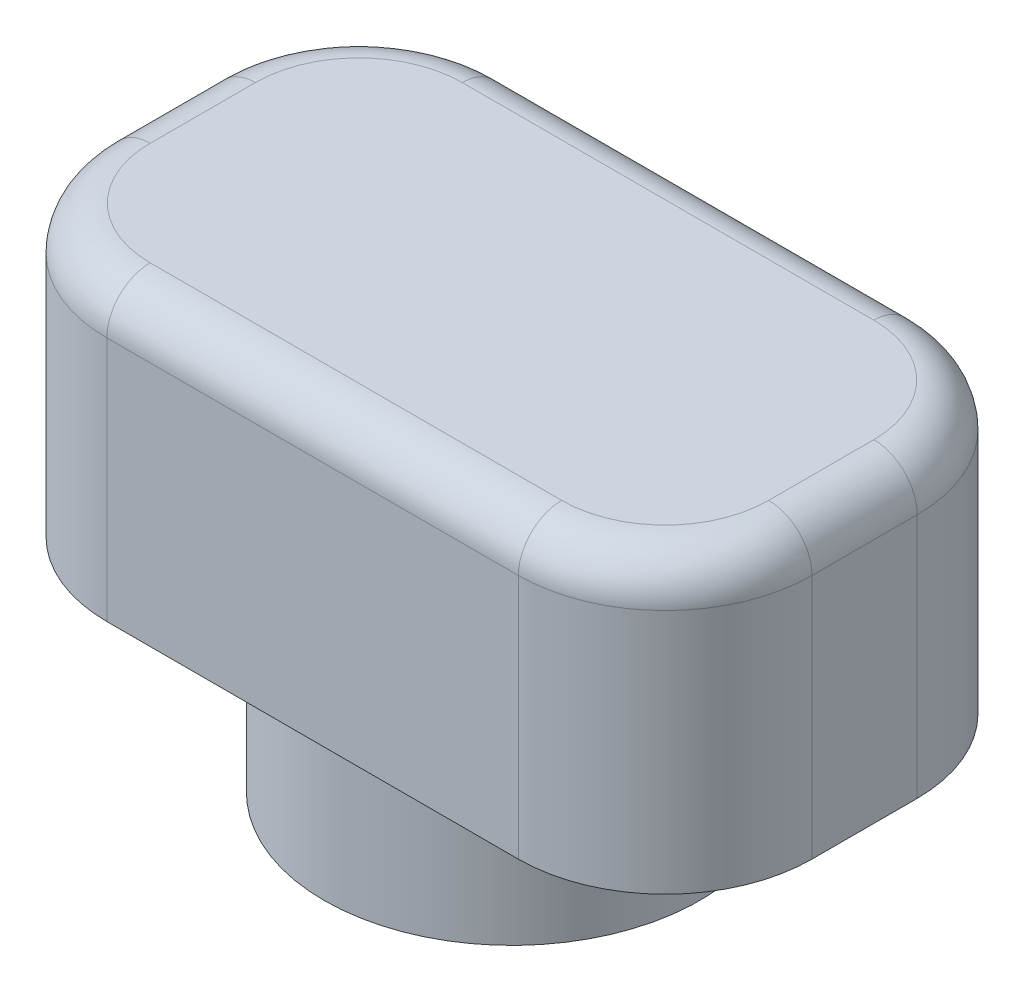
SolidWorks part; units mm, degrees
ref_plane "Front Plane" through (0, 0, 0) normal (0, 0, 1) x (1, 0, 0)
ref_plane "Top Plane" through (0, 0, 0) normal (0, 1, 0) x (1, 0, 0)
ref_plane "Right Plane" through (0, 0, 0) normal (1, 0, 0) x (0, 0, -1)
sketch "Sketch1" plane through (0, 0, 0) normal (0, 1, 0) x (1, 0, 0)
  circle A0 centre (0, 0) radius 3.25
  dimension "D1" = 6.5
extrude "Boss-Extrude1" add sketch "Sketch1" along normal blind 2.5 contours A0
sketch "Sketch2" plane through (0, 0, 0) normal (0, -1, 0) x (1, 0, 0)
  circle A1 centre (0, 0) radius 1.75
  dimension "D1" = 3.5
extrude "Cut-Extrude1" cut sketch "Sketch2" against normal blind 2.5
sketch "Sketch3" plane through (0, 2.5, 0) normal (0, 1, 0) x (1, 0, 0)
  line L1 (-6.1, 3.45) -> (6.1, 3.45)
  line L2 (-6.1, 3.45) -> (-6.1, -3.45)
  line L3 (-6.1, -3.45) -> (6.1, -3.45)
  line L4 (6.1, 3.45) -> (6.1, -3.45)
  line L5 (-6.1, 3.45) -> (6.1, -3.45) construction
  line L6 (-6.1, -3.45) -> (6.1, 3.45) construction
  point P0 (0, 0)
  dimension "D1" = 12.2
  dimension "D2" = 6.9
extrude "Boss-Extrude2" add sketch "Sketch3" along normal blind 5
fillet "Fillet1" radius 2.54 4 edges at (-6.1, 5, -3.45) (6.1, 5, -3.45) (6.1, 5, 3.45) (-6.1, 5, 3.45)
fillet "Fillet2" radius 0.75 8 edges at (6.1, 7.5, 0) (5.3561, 7.5, 2.7061) (5.3561, 7.5, -2.7061) (0, 7.5, -3.45) (-5.3561, 7.5, -2.7061) (-6.1, 7.5, 0) (-5.3561, 7.5, 2.7061) (0, 7.5, 3.45)
